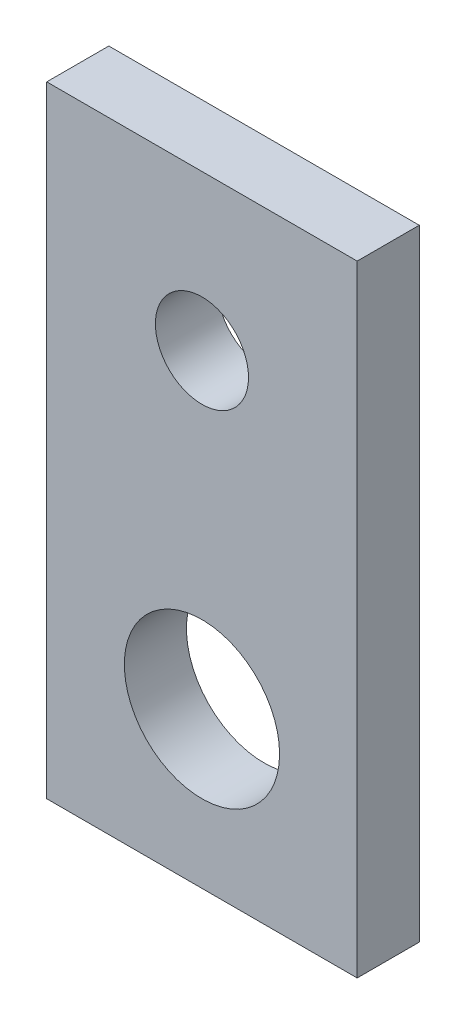
SolidWorks part; units mm, degrees
ref_plane "Plan de face" through (0, 0, 0) normal (0, 0, 1) x (1, 0, 0)
ref_plane "Plan de dessus" through (0, 0, 0) normal (0, 1, 0) x (1, 0, 0)
ref_plane "Plan de droite" through (0, 0, 0) normal (1, 0, 0) x (0, 0, -1)
sketch "Esquisse1" plane through (0, 0, 0) normal (0, 0, 1) x (1, 0, 0)
  line L1 (-10, 10) -> (0, 10)
  line L2 (-10, 10) -> (-10, -10)
  line L3 (-10, -10) -> (0, -10)
  line L4 (0, 10) -> (0, -10)
  circle A0 centre (-5, 5.0026) radius 1.5
  circle A1 centre (-5, -5) radius 2.5
  dimension "D5" = 3
  dimension "D6" = 5
  dimension "D1" = 10
  dimension "D2" = 10
  dimension "D3" = 20
  dimension "D4" = 10
  dimension "D7" = 4.9974
  dimension "D8" = 5
  dimension "D9" = 5
  dimension "D10" = 5
extrude "Boss.-Extru.1" add sketch "Esquisse1" along normal blind 2
